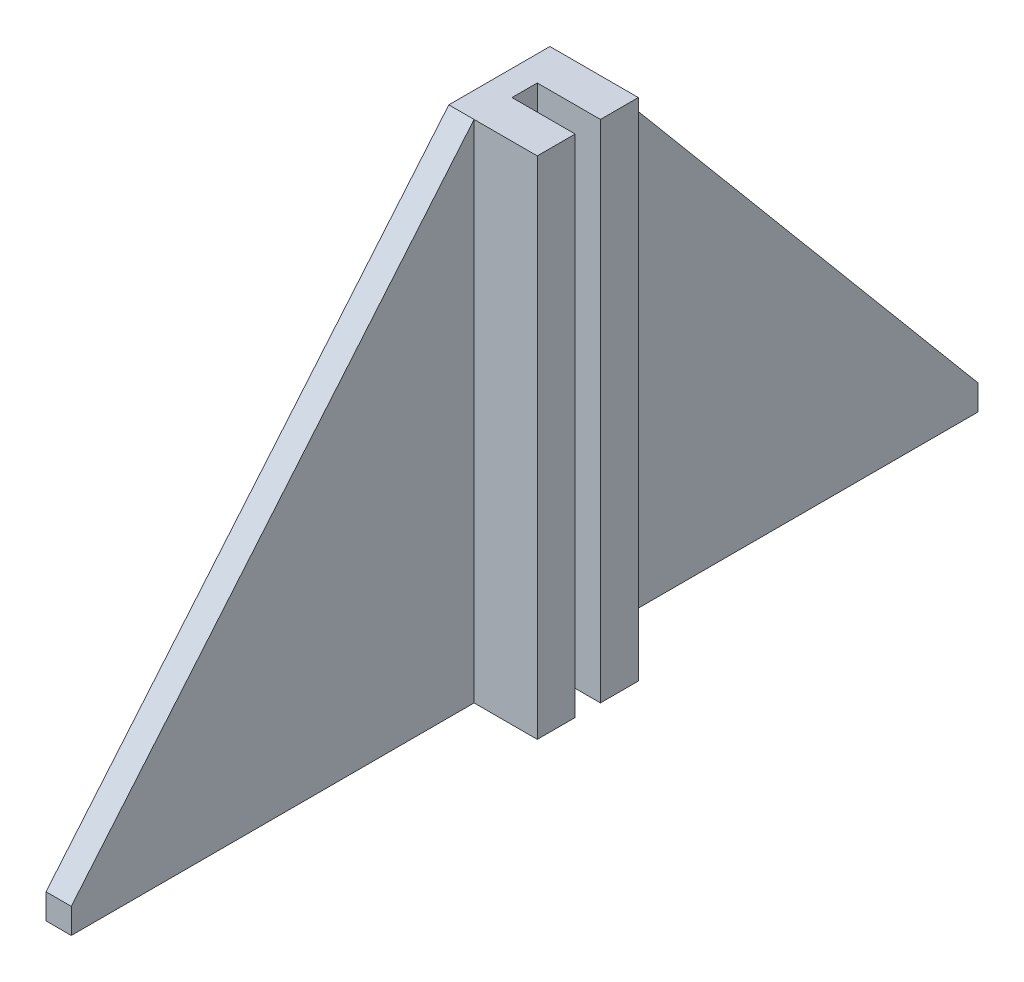
SolidWorks part; units mm, degrees
ref_plane "Front Plane" through (0, 0, 0) normal (0, 0, 1) x (1, 0, 0)
ref_plane "Top Plane" through (0, 0, 0) normal (0, 1, 0) x (1, 0, 0)
ref_plane "Right Plane" through (0, 0, 0) normal (1, 0, 0) x (0, 0, -1)
sketch "Sketch2" plane through (0, 0, 0) normal (1, 0, 0) x (0, 0, -1)
  line L0 (0, 0) -> (0, 400) construction
  line L1 (-40, 400) -> (40, 400)
  line L2 (-358.8579, 0) -> (-358.8579, 20)
  line L3 (40, 400) -> (358.8579, 20)
  line L4 (-358.8579, 0) -> (358.8579, 0)
  line L5 (358.8579, 0) -> (358.8579, 20)
  line L6 (-40, 400) -> (-358.8579, 20)
  dimension "D1" = 400
  dimension "D2" = 40
  dimension "D3" = 50
  dimension "D4" = 20
extrude "Boss-Extrude1" add sketch "Sketch2" along normal blind 20
sketch "Sketch3" plane through (20, 0, 0) normal (1, 0, 0) x (0, 0, -1)
  line L0 (-40, 400) -> (-10, 400)
  line L1 (40, 400) -> (-40, 400) construction
  line L2 (-10, 400) -> (-10, 0)
  line L3 (-358.8579, 0) -> (358.8579, 0) construction
  line L4 (-40, 400) -> (-40, 0)
  line L5 (-40, 0) -> (-10, 0)
  line L6 (40, 400) -> (10, 400)
  line L7 (10, 0) -> (40, 0)
  line L8 (40, 0) -> (40, 400)
  line L9 (10, 400) -> (10, 0)
  dimension "D1" = 30
  dimension "D2" = 30
extrude "Boss-Extrude2" add sketch "Sketch3" along normal blind 50
